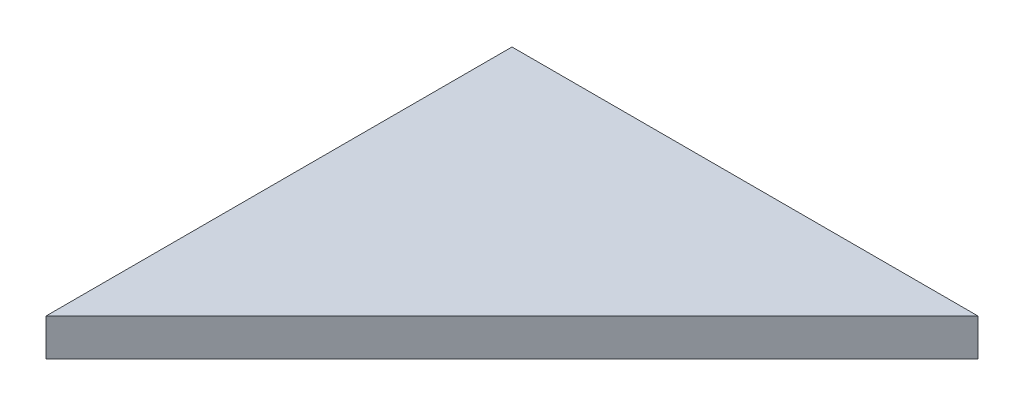
SolidWorks part; units mm, degrees
ref_plane "Front Plane" through (0, 0, 0) normal (0, 0, 1) x (1, 0, 0)
ref_plane "Top Plane" through (0, 0, 0) normal (0, 1, 0) x (1, 0, 0)
ref_plane "Right Plane" through (0, 0, 0) normal (1, 0, 0) x (0, 0, -1)
ref_plane "Plane1" through (0, 6.4, 0) normal (0, 1, 0) x (1, 0, 0)
sketch "Sketch1" plane through (0, 6.4, 0) normal (0, 1, 0) x (1, 0, 0)
  line L0 (0, 100) -> (0, 20)
  line L1 (0, 20) -> (80, 100)
  line L2 (80, 100) -> (0, 100)
extrude "Boss-Extrude1" add sketch "Sketch1" against normal blind 6.4
